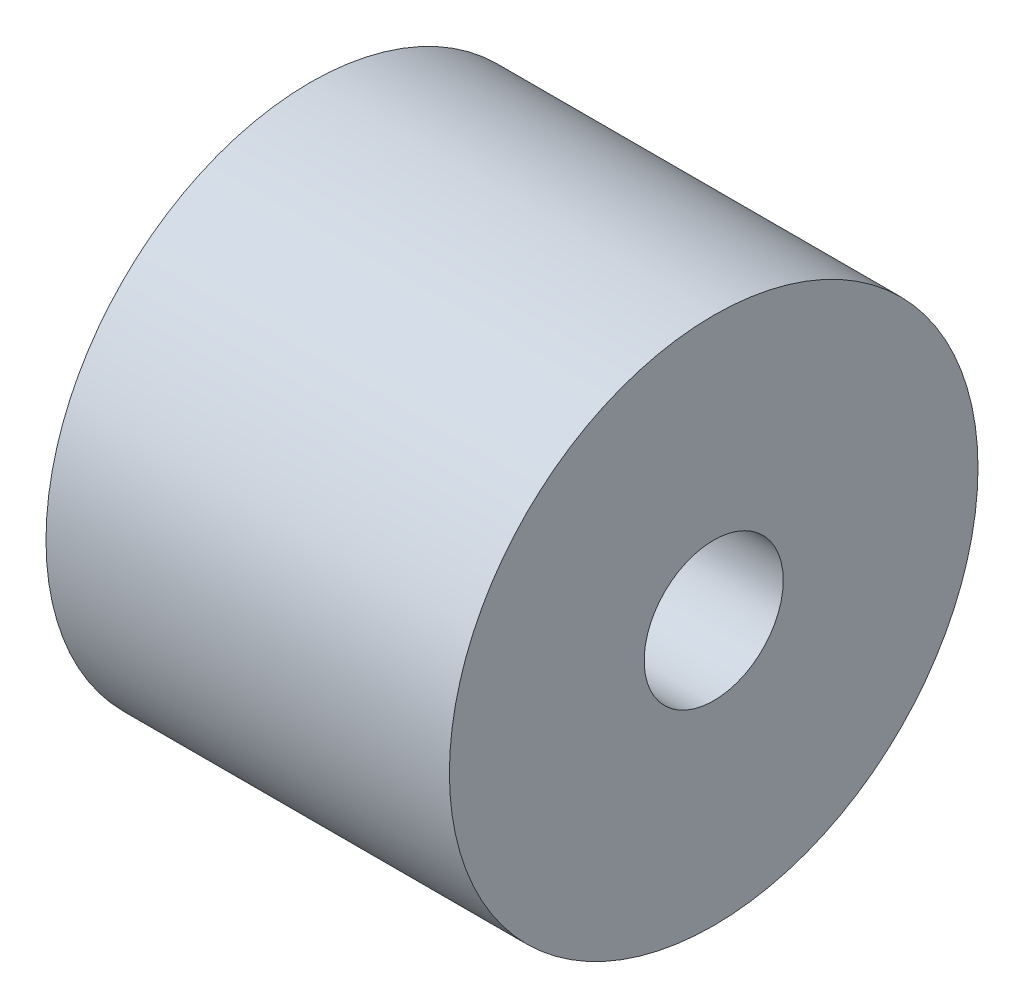
SolidWorks part; units mm, degrees
ref_plane "Front Plane" through (0, 0, 0) normal (0, 0, 1) x (1, 0, 0)
ref_plane "Top Plane" through (0, 0, 0) normal (0, 1, 0) x (1, 0, 0)
ref_plane "Right Plane" through (0, 0, 0) normal (1, 0, 0) x (0, 0, -1)
sketch "Sketch1" plane through (0, 0, 0) normal (1, 0, 0) x (0, 0, -1)
  circle A0 centre (0, 0) radius 38
  dimension "D1" = 76
extrude "OuterCircumference" add sketch "Sketch1" along normal blind 58
sketch "Sketch2" plane through (58, 0, 0) normal (1, 0, 0) x (0, 0, -1)
  circle A0 centre (0, 0) radius 11 construction
  circle A1 centre (0, 0) radius 10
  dimension "D1" = 22
  dimension "D2" = 1
extrude "Cut-Extrude2" cut sketch "Sketch2" against normal through all
